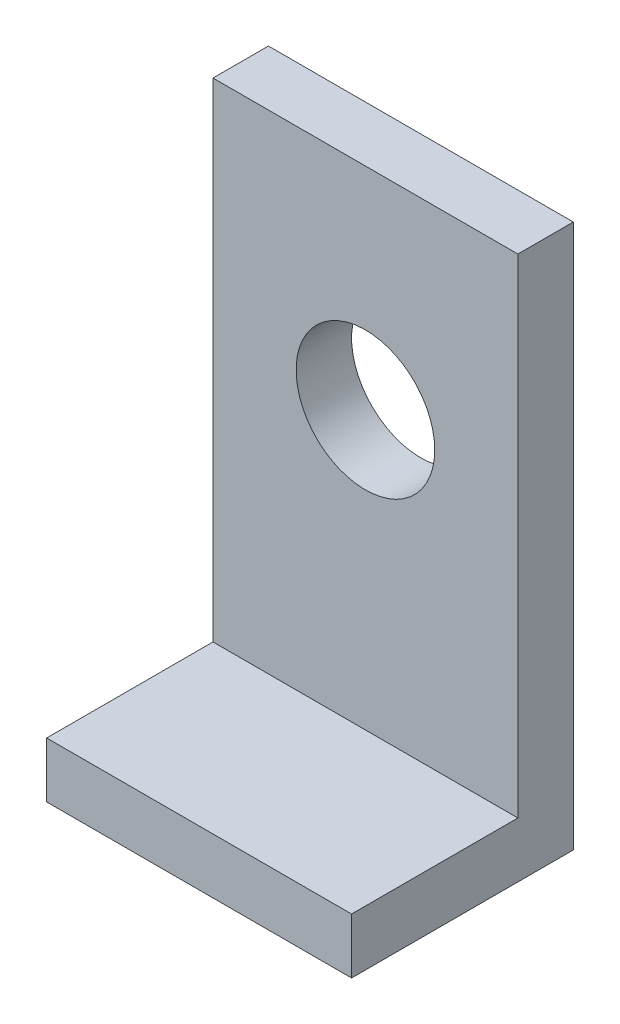
SolidWorks part; units mm, degrees
ref_plane "Alzado" through (0, 0, 0) normal (0, 0, 1) x (1, 0, 0)
ref_plane "Planta" through (0, 0, 0) normal (0, 1, 0) x (1, 0, 0)
ref_plane "Vista lateral" through (0, 0, 0) normal (1, 0, 0) x (0, 0, -1)
sketch "Croquis1" plane through (0, 0, 0) normal (0, 0, 1) x (1, 0, 0)
  line L0 (0, 0) -> (0, 98.1) construction
  line L1 (0, 98.1) -> (27.5, 98.1)
  line L2 (27.5, 98.1) -> (27.5, 0)
  line L3 (27.5, 0) -> (-27.5, 0)
  line L4 (-27.5, 0) -> (-27.5, 98.1)
  line L5 (-27.5, 98.1) -> (0, 98.1)
  circle A0 centre (0, 60) radius 12.5
  dimension "D4" = 25
  dimension "D1" = 55
  dimension "D2" = 98.1
  dimension "D3" = 60
extrude "Saliente-Extruir1" add sketch "Croquis1" along normal blind 10
sketch "Croquis2" plane through (0, 0, 10) normal (0, 0, 1) x (1, 0, 0)
  line L0 (-27.5, 0) -> (-27.5, 10)
  line L1 (-27.5, 98.1) -> (-27.5, 0) construction
  line L2 (-27.5, 10) -> (27.5, 10)
  line L3 (27.5, 0) -> (27.5, 98.1) construction
  line L4 (27.5, 10) -> (27.5, 0)
  line L5 (27.5, 0) -> (-27.5, 0)
  dimension "D1" = 10
extrude "Saliente-Extruir2" add sketch "Croquis2" along normal blind 30
